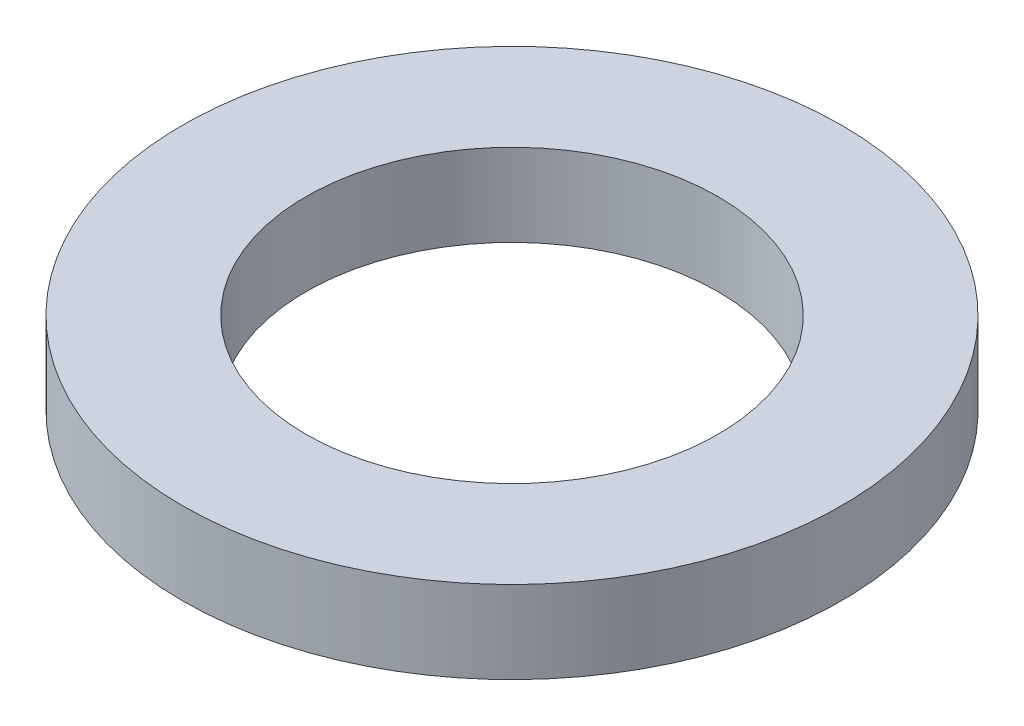
SolidWorks part; units mm, degrees
material "AISI 304"
ref_plane "Front Plane" through (0, 0, 0) normal (0, 0, 1) x (1, 0, 0)
ref_plane "Top Plane" through (0, 0, 0) normal (0, 1, 0) x (1, 0, 0)
ref_plane "Right Plane" through (0, 0, 0) normal (1, 0, 0) x (0, 0, -1)
sketch "Sketch1" plane through (0, 0, 0) normal (0, 1, 0) x (1, 0, 0)
  circle A0 centre (0, 0) radius 4
  circle A1 centre (0, 0) radius 2.5
  dimension "D1" = 5
  dimension "D2" = 8
extrude "Boss-Extrude1" add sketch "Sketch1" along normal blind 1
